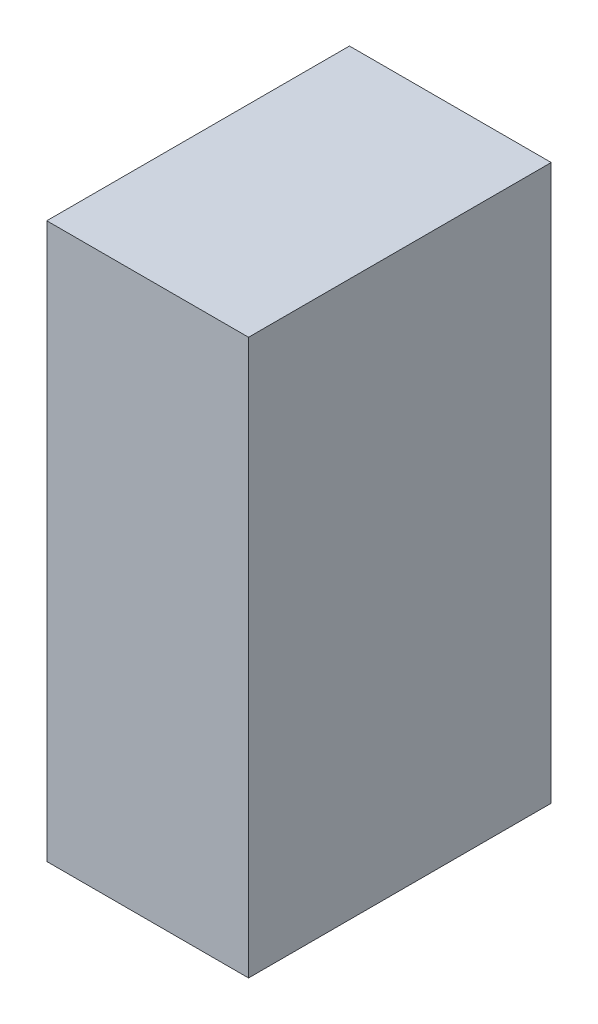
SolidWorks part; units mm, degrees
material "Balsa"
ref_plane "Piano frontale" through (0, 0, 0) normal (0, 0, 1) x (1, 0, 0)
ref_plane "Piano superiore" through (0, 0, 0) normal (0, 1, 0) x (1, 0, 0)
ref_plane "Piano destro" through (0, 0, 0) normal (1, 0, 0) x (0, 0, -1)
sketch "Schizzo1" plane through (0, 0, 0) normal (0, 1, 0) x (1, 0, 0)
  line L1 (-20, -30) -> (20, -30)
  line L2 (-20, -30) -> (-20, 30)
  line L3 (-20, 30) -> (20, 30)
  line L4 (20, -30) -> (20, 30)
  line L5 (-20, -30) -> (20, 30) construction
  line L6 (-20, 30) -> (20, -30) construction
  point P0 (0, 0)
  dimension "D1" = 40
  dimension "D2" = 60
extrude "Estrusione-Estrusione1" add sketch "Schizzo1" along normal blind 110
